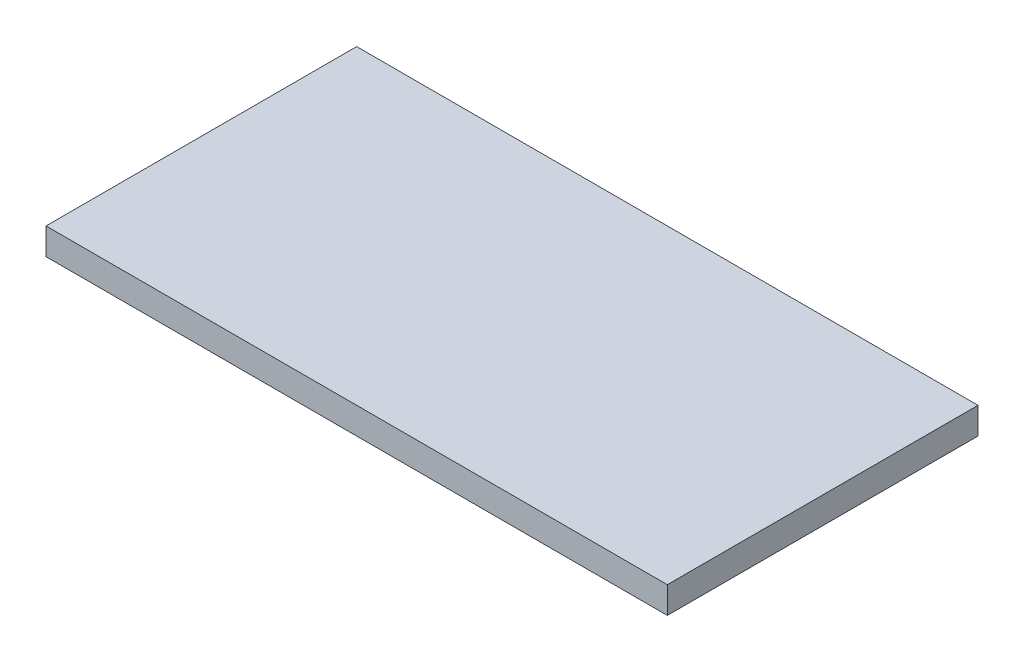
SolidWorks part; units mm, degrees
ref_plane "Спереди" through (0, 0, 0) normal (0, 0, 1) x (1, 0, 0)
ref_plane "Сверху" through (0, 0, 0) normal (0, 1, 0) x (1, 0, 0)
ref_plane "Справа" through (0, 0, 0) normal (1, 0, 0) x (0, 0, -1)
sketch "Эскиз1" plane through (0, 0, 0) normal (0, 1, 0) x (1, 0, 0)
  line L1 (0, 0) -> (700, 0)
  line L2 (0, 0) -> (0, 350)
  line L3 (0, 350) -> (700, 350)
  line L4 (700, 0) -> (700, 350)
extrude "Бобышка-Вытянуть1" add sketch "Эскиз1" along normal blind 30
